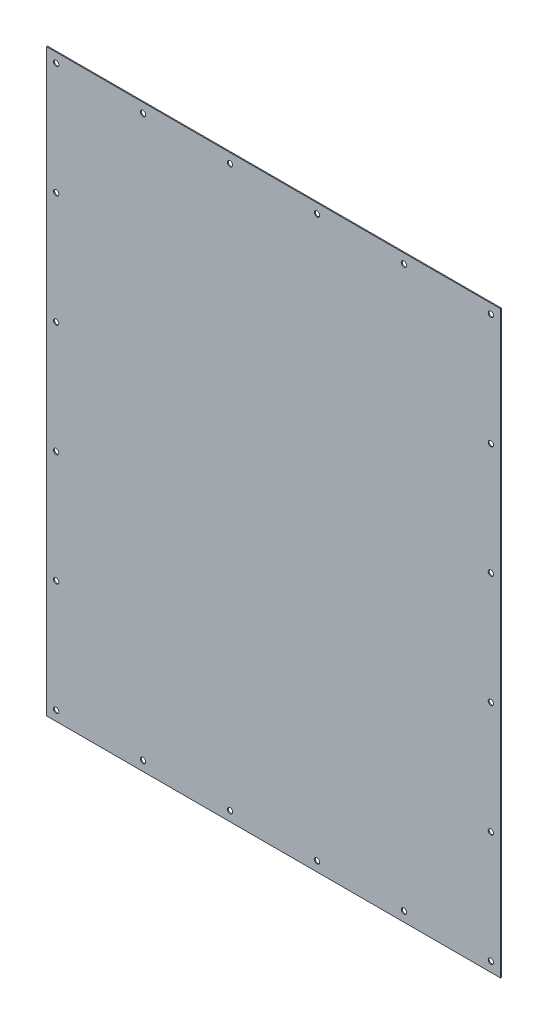
SolidWorks part; units mm, degrees
ref_plane "정면" through (0, 0, 0) normal (0, 0, 1) x (1, 0, 0)
ref_plane "윗면" through (0, 0, 0) normal (0, 1, 0) x (1, 0, 0)
ref_plane "우측면" through (0, 0, 0) normal (1, 0, 0) x (0, 0, -1)
sketch "스케치1" plane through (0, 0, 0) normal (0, 0, 1) x (1, 0, 0)
  line L1 (-235, -300) -> (235, -300)
  line L2 (-235, -300) -> (-235, 300)
  line L3 (-235, 300) -> (235, 300)
  line L4 (235, -300) -> (235, 300)
  line L5 (-235, -300) -> (235, 300) construction
  line L6 (-235, 300) -> (235, -300) construction
  line L7 (-225, -290) -> (225, -290) construction
  line L8 (-225, -290) -> (-225, 290) construction
  line L9 (-225, 290) -> (225, 290) construction
  line L10 (225, -290) -> (225, 290) construction
  line L11 (-225, -290) -> (225, 290) construction
  line L12 (-225, 290) -> (225, -290) construction
  point P0 (0, 0)
  point P6 (0, 0)
  point P12 (-225, 290)
  point P13 (225, 290)
  point P14 (225, -290)
  point P15 (-225, -290)
  point P16 (-45, -290)
  point P17 (45, -290)
  point P18 (-135, -290)
  point P19 (135, -290)
  point P20 (-225, 58)
  point P22 (-45, 290)
  point P23 (45, 290)
  point P24 (-135, 290)
  point P25 (135, 290)
  point P27 (0, 290)
  point P28 (-225, -58)
  point P29 (-225, 174)
  point P30 (-225, -174)
  point P31 (0, 0)
  point P32 (225, 58)
  point P34 (225, -58)
  point P35 (225, 174)
  point P36 (225, -174)
  point P37 (90, -290)
  point P38 (180, -290)
  point P39 (0, 0)
  point P40 (0, 0)
  point P41 (0, 0)
  point P42 (0, 0)
  point P43 (0, 0)
  point P44 (0, 0)
  point P45 (0, 0)
  point P46 (0, 0)
  point P47 (0, 0)
  point P48 (0, 0)
  point P49 (0, 0)
  point P50 (0, 0)
  point P51 (0, 0)
  point P52 (0, 0)
  point P53 (0, 0)
  point P54 (0, 0)
  point P55 (0, 0)
  point P56 (0, 0)
  dimension "D1" = 470
  dimension "D2" = 600
  dimension "D3" = 10
  dimension "D4" = 10
  dimension "D5" = 90
  dimension "D6" = 90
  dimension "D7" = 90
  dimension "D8" = 90
  dimension "D9" = 116
  dimension "a" = 116
  dimension "D10" = 116
  dimension "D11" = 116
extrude "보스-돌출1" add sketch "스케치1" along normal blind 1 contours L3 L4 L1 L2
hole_wizard "M5 여유 구멍1" positions "스케치3" profile "스케치4" hole size "M5" standard "KS" end condition through all
sketch "스케치3" plane through (0, 0, 1) normal (0, 0, 1) x (1, 0, 0)
  point P0 (-225, 290)
  point P3 (-135, 290)
  point P6 (-45, 290)
  point P9 (45, 290)
  point P12 (135, 290)
  point P15 (225, 290)
  point P18 (225, 174)
  point P21 (225, 58)
  point P24 (225, -58)
  point P27 (225, -174)
  point P30 (225, -290)
  point P33 (135, -290)
  point P36 (45, -290)
  point P39 (-45, -290)
  point P42 (-135, -290)
  point P45 (-225, -290)
  point P48 (-225, -174)
  point P51 (-225, -58)
  point P54 (-225, 174)
  point P57 (-225, 58)
sketch "스케치4" plane through (-225, 290, 1) normal (1, 0, 0) x (0, -1, 0)
  line L0 (0, 0) -> (0, 1)
  line L1 (0, 1) -> (2.75, 1)
  line L2 (2.75, 1) -> (2.75, 0)
  line L5 (2.75, 0) -> (0, 0)
  line L11 (0, -6.35) -> (0, 107.95) construction
  dimension "관통 구멍 지름" = 5.5
  dimension "관통 구멍 깊이" = 1
